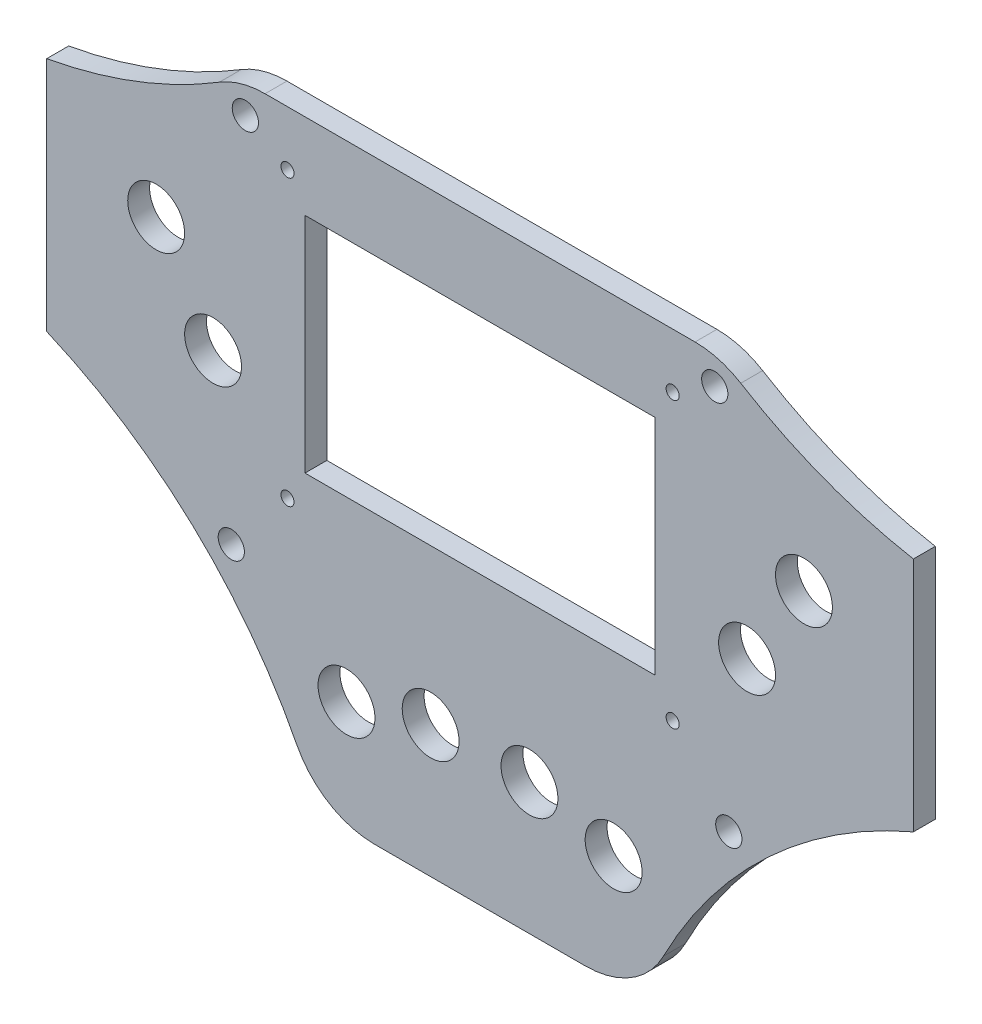
SolidWorks part; units mm, degrees
ref_plane "Plano frontal" through (0, 0, 0) normal (0, 0, 1) x (1, 0, 0)
ref_plane "Plano superior" through (0, 0, 0) normal (0, 1, 0) x (1, 0, 0)
ref_plane "Plano direito" through (0, 0, 0) normal (1, 0, 0) x (0, 0, -1)
sketch "Esboço1" plane through (0, 0, 0) normal (0, 0, 1) x (1, 0, 0)
  line L0 (-49.1191, 68) -> (49.1191, 68)
  line L1 (-74, -68) -> (-99, -68) construction
  line L3 (-24.2376, -63) -> (24.2376, -63) construction
  line L4 (99, -68) -> (99, 68) construction
  line L5 (-44, 55.5) -> (44, 55.5) construction
  line L6 (-44, -9.5) -> (-44, 55.5) construction
  line L7 (-88.0945, 47.3219) -> (-88.0945, 52.54) construction
  line L8 (-24.1062, -68) -> (24.1062, -68)
  line L9 (99, 23) -> (-99, 23) construction
  line L10 (99, -4) -> (99, 50)
  line L11 (0, 23) -> (-40, 48.5) construction
  line L12 (74, 4.761) -> (74, -18.639) construction
  line L13 (74, -68) -> (74, 68) construction
  line L14 (-46.5, -12) -> (-46.5, 58) construction
  line L15 (0, 23) -> (-46.5, -12) construction
  line L16 (74, 57.5676) -> (74, 31.1676) construction
  line L17 (-54.2891, -38) -> (-11.2891, -38) construction
  line L18 (-50.5142, -43) -> (-30.5142, -43) construction
  line L19 (-88.1314, -3.7131) -> (-88.1314, -9.3321) construction
  line L20 (-88.1314, -9.3321) -> (-88.1314, -3.7131) construction
  line L21 (74, 31.1676) -> (74, 4.761) construction
  line L22 (88.1314, -9.3321) -> (88.1314, -3.7131) construction
  line L23 (-74, 31.1676) -> (-74, 4.761) construction
  line L24 (88.1314, -3.7131) -> (88.1314, -9.3321) construction
  line L25 (-40, 48.5) -> (40, 48.5)
  line L26 (-74, 57.5676) -> (-74, 31.1676) construction
  line L27 (-74, -68) -> (-74, 68) construction
  line L28 (-74, 4.761) -> (-74, -18.639) construction
  line L29 (0, 68) -> (0, -68) construction
  line L30 (-99, -68) -> (-99, 68) construction
  line L31 (50.5142, -43) -> (30.5142, -43) construction
  line L32 (-40, -2.5) -> (-40, 48.5)
  line L33 (54.2891, -38) -> (11.2891, -38) construction
  line L34 (0, 23) -> (46.5, -12) construction
  line L35 (-46.5, -12) -> (46.5, -12) construction
  line L36 (-99, -4) -> (-99, 50)
  line L37 (-46.5, 58) -> (46.5, 58) construction
  line L38 (46.5, -12) -> (46.5, 58) construction
  line L39 (-41.2651, 62.9464) -> (41.2651, 62.9464) construction
  line L42 (-40, -2.5) -> (40, -2.5)
  line L45 (40, -2.5) -> (40, 48.5)
  line L47 (0, 23) -> (40, 48.5) construction
  line L48 (88.0945, 47.3219) -> (88.0945, 52.54) construction
  line L49 (-44, -9.5) -> (44, -9.5) construction
  line L53 (44, -9.5) -> (44, 55.5) construction
  line L54 (-24.1062, -68) -> (24.1062, -68) construction
  line L55 (74, -68) -> (99, -68) construction
  arc A0 (-49.5046, 58.613) -> (-55.6588, 56.879) centre (-53.6243, 61.4464) cw construction
  arc A1 (99, 50) -> (59.5611, 65.0577) centre (119.6025, 163.1395) cw
  arc A2 (-51.1834, -34.0488) -> (-52.2174, -26.9468) centre (-45.7528, -29.6318) cw construction
  arc A3 (41.8901, -57.1507) -> (99, -4) centre (144.147, -109.7674) cw
  circle A4 centre (74, 31.1676) radius 6.5
  arc A5 (-50.4763, -34.9265) -> (-51.1834, -34.0488) centre (-144.2784, -109.7674) ccw construction
  arc A6 (-37.5755, -54.863) -> (-50.4763, -34.9265) centre (-144.2784, -109.7674) ccw construction
  circle A7 centre (61, 11.261) radius 6.5
  arc A8 (-24.2376, -63) -> (-37.5755, -54.863) centre (-24.2376, -48) cw construction
  arc A9 (-49.5046, 58.613) -> (-41.2651, 62.9464) centre (-41.2651, 52.9464) cw construction
  circle A10 centre (11.2891, -38) radius 6.5
  circle A11 centre (30.5142, -43) radius 6.5
  arc A12 (-65.6729, -19.0968) -> (-58.6068, -20.3533) centre (-61.0875, -13.8076) ccw construction
  arc A13 (-64.3407, 56.6167) -> (-55.6588, 56.879) centre (-59.7277, 47.7442) cw construction
  arc A14 (24.1062, -68) -> (41.8901, -57.1507) centre (24.1062, -48) ccw
  arc A15 (59.5611, 65.0577) -> (49.1191, 68) centre (49.1191, 48) ccw
  arc A16 (-65.6729, -19.0968) -> (-88.1314, -3.7131) centre (-144.2784, -109.7674) ccw construction
  arc A17 (-88.0945, 47.3219) -> (-64.3407, 56.6167) centre (-119.697, 163.0858) ccw construction
  arc A18 (-58.6068, -20.3533) -> (-52.2174, -26.9468) centre (-56.8349, -25.0288) cw construction
  circle A19 centre (-53.6243, 61.4464) radius 3
  circle A20 centre (-56.8349, -25.0288) radius 3
  circle A21 centre (-44, 55.5) radius 1.5
  circle A22 centre (-44, -9.5) radius 1.5
  arc A23 (-59.5611, 65.0577) -> (-49.1191, 68) centre (-49.1191, 48) cw
  arc A24 (58.6068, -20.3533) -> (52.2174, -26.9468) centre (56.8349, -25.0288) ccw construction
  arc A25 (88.0945, 47.3219) -> (64.3407, 56.6167) centre (119.697, 163.0858) cw construction
  arc A26 (65.6729, -19.0968) -> (88.1314, -3.7131) centre (144.2784, -109.7674) cw construction
  arc A27 (64.3407, 56.6167) -> (55.6588, 56.879) centre (59.7277, 47.7442) ccw construction
  arc A28 (65.6729, -19.0968) -> (58.6068, -20.3533) centre (61.0875, -13.8076) cw construction
  arc A29 (49.5046, 58.613) -> (41.2651, 62.9464) centre (41.2651, 52.9464) ccw construction
  circle A30 centre (44, -9.5) radius 1.5
  arc A31 (-24.1062, -68) -> (-41.8901, -57.1507) centre (-24.1062, -48) cw
  circle A32 centre (44, 55.5) radius 1.5
  circle A33 centre (56.8349, -25.0288) radius 3
  arc A34 (24.2376, -63) -> (37.5755, -54.863) centre (24.2376, -48) ccw construction
  arc A35 (37.5755, -54.863) -> (50.4763, -34.9265) centre (144.2784, -109.7674) cw construction
  circle A36 centre (-30.5142, -43) radius 6.5
  circle A37 centre (-11.2891, -38) radius 6.5
  circle A38 centre (-61, 11.261) radius 6.5
  circle A39 centre (53.6243, 61.4464) radius 3
  arc A40 (50.4763, -34.9265) -> (51.1834, -34.0488) centre (144.2784, -109.7674) cw construction
  arc A41 (51.1834, -34.0488) -> (52.2174, -26.9468) centre (45.7528, -29.6318) ccw construction
  circle A42 centre (-74, 31.1676) radius 6.5
  arc A43 (-41.8901, -57.1507) -> (-99, -4) centre (-144.147, -109.7674) ccw
  arc A44 (-99, 50) -> (-59.5611, 65.0577) centre (-119.6025, 163.1395) ccw
  arc A46 (49.5046, 58.613) -> (55.6588, 56.879) centre (53.6243, 61.4464) ccw construction
  point P47 (0, -9.5)
  point P53 (0, 62.9464)
  point P57 (0, 58)
  point P60 (0, -12)
  point P68 (37, -68)
  point P71 (55, 68)
  point P84 (0, 23)
  point P86 (0, 23)
  point P87 (0, 55.5)
  point P88 (0, -63)
  point P99 (0, 23)
  point P107 (61.3987, -22.9863)
  point P132 (0, -2.5)
  point P133 (0, 48.5)
  point P134 (-36.3103, -68)
  point P135 (-61.3987, -22.9863)
  point P136 (-55, 68)
  point P139 (-37, -68)
  point P144 (36.3103, -68)
  dimension "D15" = 26.4
  dimension "D17" = 23.4
  dimension "D32" = 13
  dimension "D33" = 13
  dimension "D2" = 136
  dimension "D5" = 64
  dimension "D12" = 25
  dimension "D28" = 20
  dimension "D29" = 43
extrude "Ressalto-extrusão1" add sketch "Esboço1" along normal blind 5
